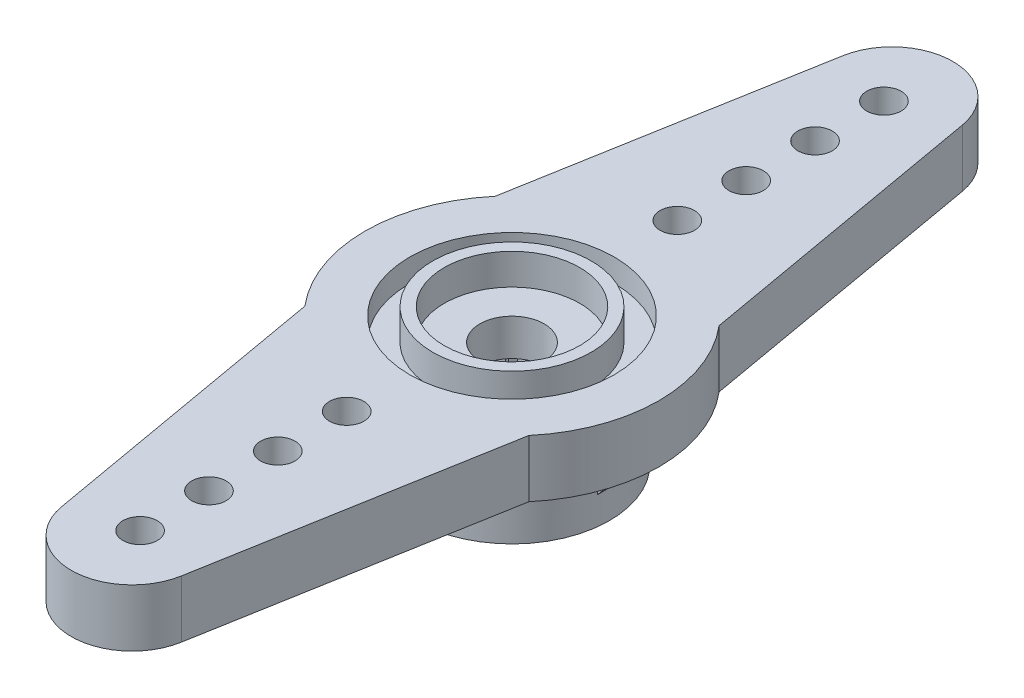
SolidWorks part; units mm, degrees
material "PC High Viscosity"
ref_plane "Front Plane" through (0, 0, 0) normal (0, 0, 1) x (1, 0, 0)
ref_plane "Top Plane" through (0, 0, 0) normal (0, 1, 0) x (1, 0, 0)
ref_plane "Right Plane" through (0, 0, 0) normal (1, 0, 0) x (0, 0, -1)
sketch "BaseS" plane through (0, 0, 0) normal (0, 1, 0) x (1, 0, 0)
  circle A0 centre (0, 0) radius 6.4
  dimension "Dia" = 12.8
extrude "BASE" add sketch "BaseS" along normal blind 5.6
sketch "TopBoreS" plane through (0, 5.6, 0) normal (0, 1, 0) x (1, 0, 0)
  circle A0 centre (0, 0) radius 1.4
  dimension "Dia" = 2.8
extrude "TOP BORE" cut sketch "TopBoreS" against normal through all
sketch "HornHalfS" plane through (0, 5.6, 0) normal (0, 1, 0) x (1, 0, 0)
  line L0 (0, 0) -> (0, 16.55) construction
  line L1 (-2.6097, 17.0102) -> (-4.8787, 4.1423)
  line L2 (0, 19.2) -> (0, 16.55) construction
  line L3 (2.6097, 17.0102) -> (4.8787, 4.1423)
  arc A0 (2.6097, 17.0102) -> (-2.6097, 17.0102) centre (0, 16.55) ccw
  arc A1 (4.8787, 4.1423) -> (-4.8787, 4.1423) centre (0, 0) ccw
  circle A2 centre (0, 0) radius 6.4 construction
  dimension "EndDia" = 5.3
  dimension "HornLength" = 19.2
  dimension "Angle" = 10
  dimension "RefWidth" = 9.7574
extrude "HORN HALF" add sketch "HornHalfS" against normal blind 2.5
sketch "HornAttachS" plane through (0, 5.6, 0) normal (0, 1, 0) x (1, 0, 0)
  line L0 (0, 19.2) -> (0, 16.2) construction
  circle A0 centre (0, 16.2) radius 0.75
  arc A1 (2.6097, 17.0102) -> (-2.6097, 17.0102) centre (0, 16.55) ccw construction
  dimension "Dia" = 1.5
  dimension "Dist" = 3
extrude "HORN ATTACH" cut sketch "HornAttachS" against normal through all
sketch "HA LP RS" plane through (0, 0, 0) normal (0, 1, 0) x (1, 0, 0)
  line L0 (0, 0) -> (0, 16.2) construction
pattern_linear "HA LP" count 4 spacing 3 along (0, 0, 1) of "HORN ATTACH"
mirror "HORN BODIES" about plane through (0, 0, 0) normal (0, 0, 1) of "HA LP", "HORN ATTACH", "HORN HALF"
sketch "ToothS" plane through (0, 0, 0) normal (0, -1, 0) x (1, 0, 0)
  line L0 (0, -2.9) -> (0.2629, -2.5867)
  line L1 (0, -2.9) -> (-0.2629, -2.5867)
  line L2 (0, -2.6) -> (0, -2.9) construction
  line L3 (0, 0) -> (0, -2.6) construction
  arc A0 (-0.2629, -2.5867) -> (0.2629, -2.5867) centre (0, 0) ccw
  dimension "D1" = 5.2
  dimension "D2" = 80
  dimension "D3" = 0.3
extrude "TOOTH" cut sketch "ToothS" against normal blind 3
pattern_circular "TOOTH CP" count 26 over 360 about axis through (0, 0, 0) along (0, 1, 0) of "TOOTH"
sketch "BottomBoreS" plane through (0, 0, 0) normal (0, -1, 0) x (-1, 0, 0)
  circle A0 centre (0, 0) radius 2.6
  arc A1 (0.2629, 2.5867) -> (-0.2629, 2.5867) centre (0, 0) ccw construction
extrude "BOTTOM BORE" cut sketch "BottomBoreS" against normal up to surface (3 mm away) up to face at (-0.6451, 3, 2.6172)
sketch "HoldingShaftS" plane through (0, 0, 0) normal (0, -1, 0) x (1, 0, 0)
  circle A0 centre (0, 0) radius 6.4 construction
  circle A1 centre (0, 0) radius 6.4
  circle A2 centre (0, 0) radius 4.25
  dimension "D1" = 2.15
  dimension "D2" = 8.5
extrude "HOLDING SHAFT" cut sketch "HoldingShaftS" against normal up to surface (3.1 mm away) up to face at (0, 3.1, -12.45)
sketch "RibS" plane through (0, 0, 0) normal (0, 0, 1) x (1, 0, 0)
  line L0 (4.21, 1.2) -> (5.8043, 3.1)
  line L1 (5.8043, 3.1) -> (4.21, 3.1)
  line L2 (4.21, 1.2) -> (4.16, 1.2)
  line L3 (4.16, 1.2) -> (4.16, 3.1)
  line L4 (4.21, 1.2) -> (4.21, 3.1) construction
  line L5 (4.16, 3.1) -> (4.21, 3.1)
  line L6 (-4.25, 3.1) -> (4.25, 3.1) construction
  line L7 (4.21, 3.1) -> (4.25, 3.1) construction
  line L8 (4.25, 0) -> (4.25, 3.1) construction
  dimension "D1" = 1.9
  dimension "D2" = 0.05
  dimension "D3" = 40
  dimension "D4" = 0.09
extrude "RIB" add sketch "RibS" along normal mid plane 1
pattern_circular "RIB CP" count 4 over 360 about axis through (0, 0, 0) along (0, 1, 0) of "RIB"
sketch "TopCutS" plane through (0, 5.6, 0) normal (0, 1, 0) x (1, 0, 0)
  circle A0 centre (0, 0) radius 4.45
  arc A1 (4.8787, -4.1423) -> (4.8787, 4.1423) centre (0, 0) ccw construction
  dimension "RefDia" = 8.9
  dimension "DiaControl" = 1.95
extrude "TOP CUT" cut sketch "TopCutS" against normal blind 1
sketch "TopPocketCylinderS" plane through (0, 4.6, 0) normal (0, 1, 0) x (1, 0, 0)
  circle A0 centre (0, 0) radius 2.95
  circle A1 centre (0, 0) radius 3.45
  circle A2 centre (0, 0) radius 4.45 construction
  dimension "RefDia" = 6.9
  dimension "Width" = 0.5
  dimension "DiaControl" = 1
extrude "TOP POCKET CYLINDER" add sketch "TopPocketCylinderS" along normal offset from surface (1.35 mm away) 0.35 up to face at (0, 5.6, 4.45) offset beyond the face yes
